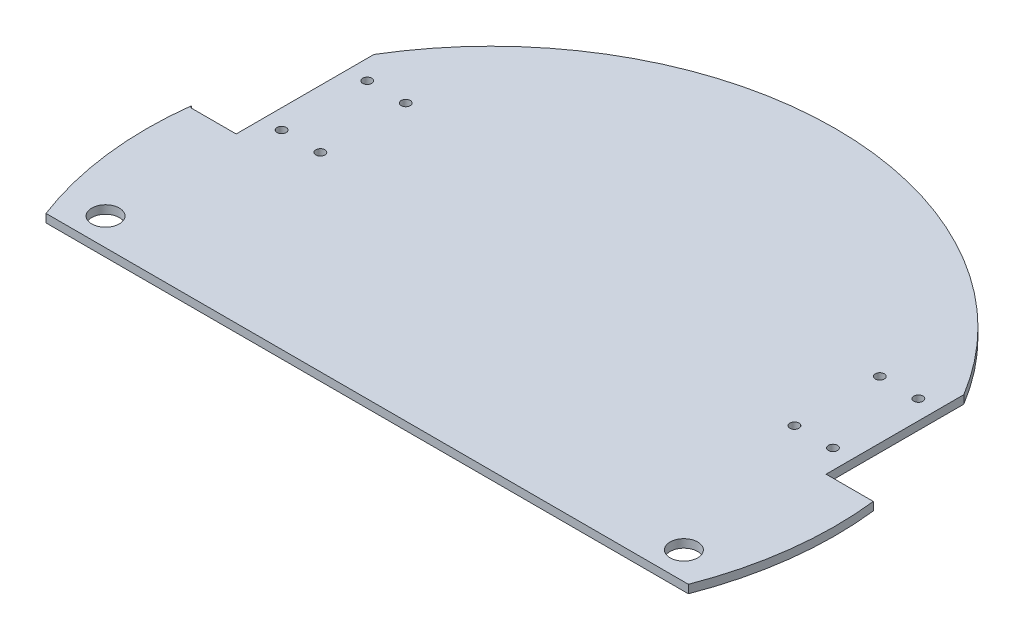
SolidWorks part; units mm, degrees
ref_plane "Front Plane" through (0, 0, 0) normal (0, 0, 1) x (1, 0, 0)
ref_plane "Top Plane" through (0, 0, 0) normal (0, 1, 0) x (1, 0, 0)
ref_plane "Right Plane" through (0, 0, 0) normal (1, 0, 0) x (0, 0, -1)
sketch "Sketch2" plane through (0, 0, 0) normal (0, 1, 0) x (1, 0, 0)
  circle A0 centre (-17.8077, -0.8549) radius 125
  dimension "D1" = 250
extrude "Boss-Extrude1" add sketch "Sketch2" along normal blind 3
sketch "Sketch3" plane through (0, 0, 0) normal (0, -1, 0) x (1, 0, 0)
  line L0 (-134.4267, 45.8549) -> (98.8114, 45.8549)
  circle A0 centre (-17.8077, 0.8549) radius 125 construction
  circle A1 centre (-17.8077, 0.8549) radius 125
  circle M2 centre (-17.8077, 0.8549) radius 125
  dimension "D1" = 45
extrude "Cut-Extrude1" cut sketch "Sketch3" against normal blind 3 contours L0 M2
sketch "Sketch4" plane through (0, 0, 0) normal (0, -1, 0) x (-1, 0, 0)
  line L0 (134.4267, -45.8549) -> (-98.8114, -45.8549) construction
  line L1 (124.8812, 63.6451) -> (124.8812, 13.6451)
  line L2 (124.8812, 13.6451) -> (141.3575, 13.6451)
  line L3 (141.3575, 13.6451) -> (159.3776, 40.4813)
  line L4 (159.3776, 40.4813) -> (124.8812, 63.6451)
  line L5 (-89.1923, 63.7671) -> (-89.1923, 13.7671)
  line L6 (-89.1923, 13.7671) -> (-106.3342, 13.7671)
  line L7 (-106.3342, 13.7671) -> (-114.0798, 54.5963)
  line L8 (-114.0798, 54.5963) -> (-89.1923, 63.7671)
  circle A0 centre (117.8077, 54.1451) radius 1.65
  circle A1 centre (117.8812, 23.1452) radius 1.65
  circle A2 centre (103.8077, 54.1451) radius 1.65
  circle A3 centre (103.8077, 23.1451) radius 1.65
  arc A4 (134.4267, -45.8549) -> (-98.8114, -45.8549) centre (17.8077, -0.8549) ccw construction
  circle A5 centre (-68.1923, 54.2671) radius 1.65
  circle A6 centre (-82.1923, 54.2671) radius 1.65
  circle A7 centre (-82.1923, 23.2671) radius 1.65
  circle A8 centre (-68.1923, 23.2671) radius 1.65
  circle A9 centre (122.8077, -35.8549) radius 5
  circle A10 centre (-87.1923, -35.8549) radius 5
  dimension "D1" = 3.3
  dimension "D3" = 31
  dimension "D8" = 14
  dimension "D10" = 105
  dimension "D11" = 105
  dimension "D2" = 100
  dimension "D4" = 31
  dimension "D5" = 0
  dimension "D6" = 14
  dimension "D7" = 100
  dimension "D9" = 100
  dimension "D12" = 10
  dimension "D13" = 10
  dimension "D14" = 50
  dimension "D15" = 7
  dimension "D16" = 7
  dimension "D17" = 14
  dimension "D18" = 31
  dimension "D19" = 0
  dimension "D20" = 50
  dimension "D21" = 9.5001
  dimension "D22" = 9.5
extrude "Cut-Extrude2" cut sketch "Sketch4" against normal blind 10
